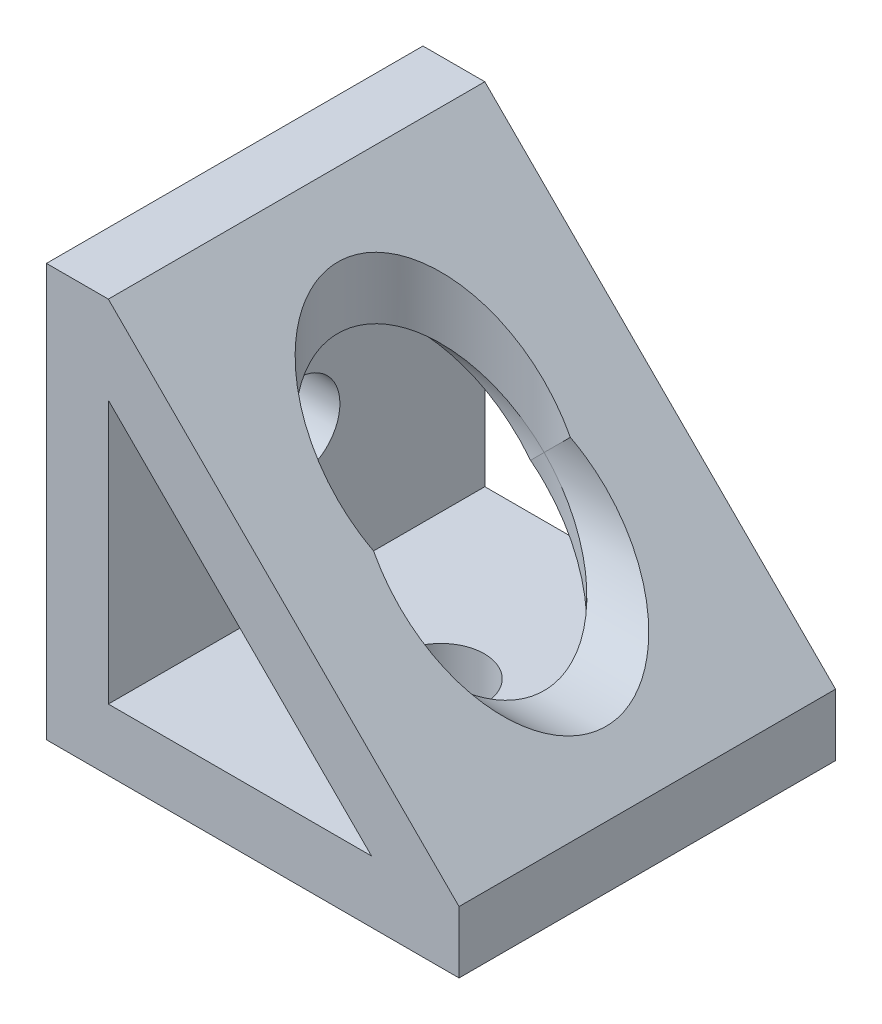
SolidWorks part; units mm, degrees
ref_plane "Front Plane" through (0, 0, 0) normal (0, 0, 1) x (1, 0, 0)
ref_plane "Top Plane" through (0, 0, 0) normal (0, 1, 0) x (1, 0, 0)
ref_plane "Right Plane" through (0, 0, 0) normal (1, 0, 0) x (0, 0, -1)
sketch "Sketch1" plane through (0, 0, 0) normal (0, 0, 1) x (1, 0, 0)
  line L0 (0, 20) -> (0, -20) construction
  line L1 (20, 0) -> (-20, 0) construction
  line L2 (-4.2, -20) -> (4.2, -20) construction
  line L3 (-20, -20) -> (-20, -14) construction
  line L4 (-10, -14) -> (10, -14) construction
  point P4 (0, 0)
  point P8 (0, 0)
  point P11 (0, -20)
  point P16 (0, -14)
  dimension "Length" = 40
  dimension "Clearance Hole" = 8.4
  dimension "Wall" = 6
  dimension "Access Hole" = 20
  dimension "For Rail Height" = 40
sketch "Sketch3" plane through (0, 0, 0) normal (1, 0, 0) x (0, 0, -1)
  line L0 (18.25, 0) -> (-18.25, 0) construction
  point P3 (0, 0)
  dimension "Thickness" = 36.5
sketch "Sketch2" plane through (0, 0, 0) normal (0, 0, 1) x (1, 0, 0)
  line L0 (-20, 20) -> (-20, -20)
  line L1 (-20, -20) -> (20, -20)
  line L3 (-4.2, -20) -> (4.2, -20) construction
  line L4 (-20, -20) -> (-20, -14) construction
  line L5 (20, -20) -> (20, -14)
  line L6 (20, -14) -> (-14, 20)
  line L7 (-14, 20) -> (-20, 20)
  line L8 (-14, 11.5147) -> (-14, -14)
  line L9 (-14, -14) -> (11.5147, -14)
  line L10 (11.5147, -14) -> (11.5147, -14)
  line L11 (11.5147, -14) -> (-14, 11.5147)
  line L12 (-14, 11.5147) -> (-14, 11.5147)
extrude "Boss-Extrude1" add sketch "Sketch2" against normal up to vertex (18.25 mm away) and the other way up to vertex (18.25 mm away) up to point (0, 0, -18.25) other way up to point (0, 0, 18.25)
sketch "Sketch4" plane through (0, -20, 0) normal (0, -1, 0) x (1, 0, 0)
  line L0 (-4.2, 0) -> (4.2, 0) construction
  line L1 (-4.2, 0) -> (4.2, 0) construction
  circle A0 centre (0, 0) radius 4.2
extrude "Cut-Extrude1" cut sketch "Sketch4" against normal up to next (6 mm away)
sketch "Sketch6" plane through (0, -14, 0) normal (0, 1, 0) x (1, 0, 0)
  circle A0 centre (0, 0) radius 10
extrude "Cut-Extrude2" cut sketch "Sketch6" along normal through all
ref_plane "Plane1" through (0, 0, 0) normal (0.7071, -0.7071, 0) x (-0.7071, -0.7071, 0)
mirror "Mirror1" about plane through (0, 0, 0) normal (0.7071, -0.7071, 0) of "Cut-Extrude2", "Cut-Extrude1"
sketch "Sketch7" plane through (0, -14, 0) normal (0, 1, 0) x (1, 0, 0)
  line L0 (0, 0) -> (3.6373, 2.1) construction
  line L1 (20, -18.25) -> (-14, -18.25) construction
  circle A0 centre (0, 0) radius 4.2 construction
  dimension "D1" = 30
sketch "Sketch8" plane through (-14, 0, 0) normal (1, 0, 0) x (0, 0, -1)
  line L0 (0, 0) -> (-2.9698, 2.9698) construction
  line L1 (18.25, -20) -> (-18.25, -20) construction
  circle A0 centre (0, 0) radius 4.2 construction
  dimension "D1" = 45
